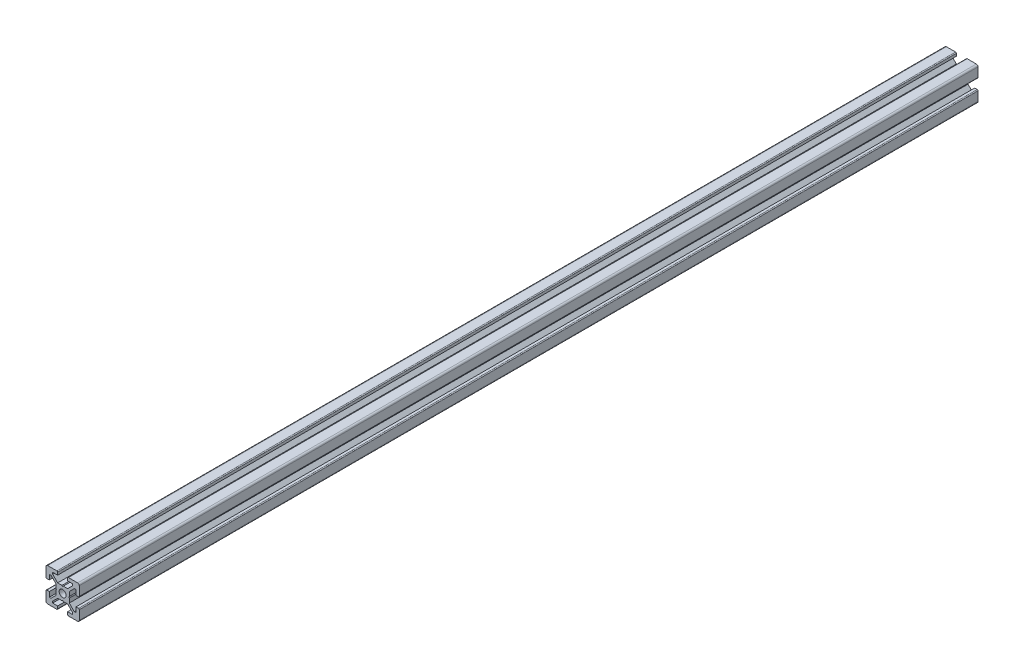
SolidWorks part; units mm, degrees
material "Lega 6061"
ref_plane "Piano frontale" through (0, 0, 0) normal (0, 0, 1) x (1, 0, 0)
ref_plane "Piano superiore" through (0, 0, 0) normal (0, 1, 0) x (1, 0, 0)
ref_plane "Piano destro" through (0, 0, 0) normal (1, 0, 0) x (0, 0, -1)
sketch "Schizzo1" plane through (0, 0, 0) normal (0, 0, 1) x (1, 0, 0)
  line L0 (0, 0) -> (-10, 0) construction
  line L1 (0, 0) -> (0, 10) construction
  line L2 (-3.6, 0) -> (-4, 0.4)
  line L3 (-4, 0.4) -> (-4, 3)
  line L4 (-4, 3) -> (-7, 6)
  line L5 (-7, 6) -> (-8, 6)
  line L6 (-8, 6) -> (-8, 3)
  line L7 (-8, 3) -> (-9.5, 3)
  line L8 (-10, 3.5) -> (-10, 9)
  line L9 (0, 0) -> (-10, 10) construction
  line L10 (0, 3.6) -> (-0.4, 4)
  line L11 (-0.4, 4) -> (-3, 4)
  line L12 (-3, 4) -> (-6, 7)
  line L13 (-6, 7) -> (-6, 8)
  line L14 (-6, 8) -> (-3, 8)
  line L15 (-3, 8) -> (-3, 9.5)
  line L16 (-3.5, 10) -> (-9, 10)
  line L17 (0, 0) -> (-10, -10) construction
  line L18 (-3.5, -10) -> (-9, -10)
  line L19 (-3, -8) -> (-3, -9.5)
  line L20 (-6, -8) -> (-3, -8)
  line L21 (-6, -7) -> (-6, -8)
  line L22 (-3, -4) -> (-6, -7)
  line L23 (-0.4, -4) -> (-3, -4)
  line L24 (0, -3.6) -> (-0.4, -4)
  line L25 (-10, -3.5) -> (-10, -9)
  line L26 (-8, -3) -> (-9.5, -3)
  line L27 (-8, -6) -> (-8, -3)
  line L28 (-7, -6) -> (-8, -6)
  line L29 (-4, -3) -> (-7, -6)
  line L30 (-4, -0.4) -> (-4, -3)
  line L31 (-3.6, 0) -> (-4, -0.4)
  line L32 (0, 0) -> (10, -10) construction
  line L33 (0, 0) -> (10, 10) construction
  line L34 (3.6, 0) -> (4, -0.4)
  line L35 (4, -0.4) -> (4, -3)
  line L36 (4, -3) -> (7, -6)
  line L37 (7, -6) -> (8, -6)
  line L38 (8, -6) -> (8, -3)
  line L39 (8, -3) -> (9.5, -3)
  line L40 (10, -3.5) -> (10, -9)
  line L41 (0, -3.6) -> (0.4, -4)
  line L42 (0.4, -4) -> (3, -4)
  line L43 (3, -4) -> (6, -7)
  line L44 (6, -7) -> (6, -8)
  line L45 (6, -8) -> (3, -8)
  line L46 (3, -8) -> (3, -9.5)
  line L47 (3.5, -10) -> (9, -10)
  line L48 (3.5, 10) -> (9, 10)
  line L49 (3, 8) -> (3, 9.5)
  line L50 (6, 8) -> (3, 8)
  line L51 (6, 7) -> (6, 8)
  line L52 (3, 4) -> (6, 7)
  line L53 (0.4, 4) -> (3, 4)
  line L54 (0, 3.6) -> (0.4, 4)
  line L55 (10, 3.5) -> (10, 9)
  line L56 (8, 3) -> (9.5, 3)
  line L57 (8, 6) -> (8, 3)
  line L58 (7, 6) -> (8, 6)
  line L59 (4, 3) -> (7, 6)
  line L60 (4, 0.4) -> (4, 3)
  line L61 (3.6, 0) -> (4, 0.4)
  arc A0 (-10, 9) -> (-9, 10) centre (-9, 9) cw
  arc A1 (-3, 9.5) -> (-3.5, 10) centre (-3.5, 9.5) ccw
  arc A2 (-9.5, 3) -> (-10, 3.5) centre (-9.5, 3.5) cw
  arc A3 (-9.5, -3) -> (-10, -3.5) centre (-9.5, -3.5) ccw
  arc A4 (-3, -9.5) -> (-3.5, -10) centre (-3.5, -9.5) cw
  arc A5 (-10, -9) -> (-9, -10) centre (-9, -9) ccw
  arc A6 (10, -9) -> (9, -10) centre (9, -9) cw
  arc A7 (3, -9.5) -> (3.5, -10) centre (3.5, -9.5) ccw
  arc A8 (9.5, -3) -> (10, -3.5) centre (9.5, -3.5) cw
  arc A9 (9.5, 3) -> (10, 3.5) centre (9.5, 3.5) ccw
  arc A10 (3, 9.5) -> (3.5, 10) centre (3.5, 9.5) cw
  arc A11 (10, 9) -> (9, 10) centre (9, 9) ccw
  circle A12 centre (0, 0) radius 2.1
  point P24 (-3, 10)
  point P27 (-10, 3)
  point P49 (-10, -3)
  point P50 (-3, -10)
  point P92 (3, -10)
  point P93 (10, -3)
  point P94 (10, 3)
  point P95 (3, 10)
  dimension "D2" = 1
  dimension "D12" = 0.5
  dimension "D13" = 4.2
  dimension "D3" = 8
  dimension "D4" = 0.4
  dimension "D5" = 45
  dimension "D6" = 6
  dimension "D7" = 12
  dimension "D8" = 20
  dimension "D9" = 2
  dimension "D10" = 4
  dimension "D11" = 45
extrude "Estrusione-Estrusione1" add sketch "Schizzo1" along normal blind 540
